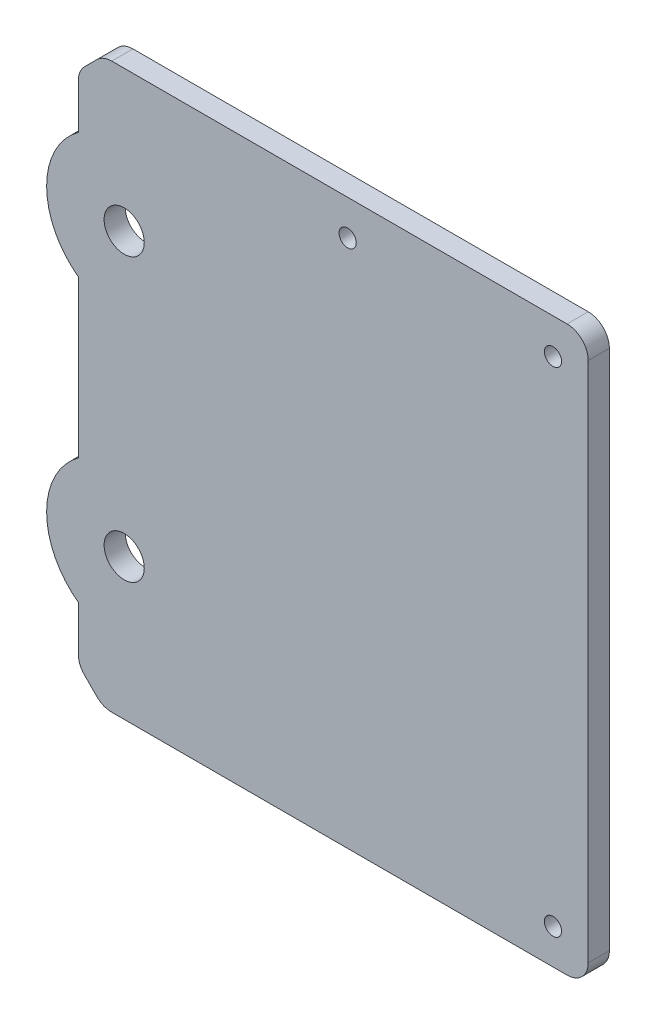
SolidWorks part; units mm, degrees
ref_plane "Front Plane" through (0, 0, 0) normal (0, 0, 1) x (1, 0, 0)
ref_plane "Top Plane" through (0, 0, 0) normal (0, 1, 0) x (1, 0, 0)
ref_plane "Right Plane" through (0, 0, 0) normal (1, 0, 0) x (0, 0, -1)
sketch "Base" plane through (0, 0, 0) normal (0, 0, 1) x (1, 0, 0)
  line L1 (-29.1058, 40) -> (-29.1058, -40)
  line L4 (-17.7758, -40) -> (43.2242, -40)
  line L8 (-22.6058, 20) -> (-22.6058, -20) construction
  line L9 (12.7242, 15.875) -> (12.7242, -32.625) construction
  line L10 (23.8492, 12.75) -> (1.5992, 12.75)
  line L11 (23.8492, 12.75) -> (23.8492, -29.5)
  line L12 (23.8492, -29.5) -> (1.5992, -29.5)
  line L13 (1.5992, 12.75) -> (1.5992, -29.5)
  line L14 (33.2242, 30) -> (33.2242, -30) construction
  line L15 (33.2242, 1) -> (43.2242, 1) construction
  line L16 (43.2242, 40) -> (43.2242, -40)
  line L18 (-17.7758, -40) -> (-29.1058, -40)
  line L19 (33.2242, -30) -> (33.2242, -40) construction
  line L20 (33.2242, 30) -> (43.2242, 40) construction
  line L21 (-29.1058, 40) -> (43.2242, 40)
  line L22 (7.7242, -32.625) -> (17.7242, -32.625)
  line L24 (33.2242, 30) -> (1.5992, 30) construction
  line L25 (1.5992, 30) -> (1.5992, 40) construction
  line L26 (1.5992, -40) -> (1.5992, -30) construction
  line L27 (1.5992, -30) -> (33.2242, -30) construction
  line L28 (7.7242, 15.875) -> (17.7242, 15.875)
  circle A0 centre (12.7242, -20) radius 17.5 construction
  point P2 (30.2242, -20)
  point P7 (24.1741, 0)
  point P9 (12.7242, -40)
  point P10 (-29.1058, 0)
  point P11 (-22.6058, -20)
  point P12 (-22.6058, 20)
  point P15 (-22.6058, 0)
  point P20 (12.7242, 12.75)
  point P22 (23.8492, -8.375)
  point P23 (12.7242, 20)
  point P24 (-22.6058, -20)
  point P25 (-22.6058, 20)
  point P26 (12.7242, 15.875)
  point P27 (12.7242, -32.625)
  point P30 (12.7242, -8.375)
  point P31 (12.7242, -20)
  point P33 (12.7242, -2.5)
  point P41 (38.2242, -35)
  point P43 (38.2242, 35)
  point P44 (9.0992, 35)
  point P45 (1.5992, 35)
  point P46 (38.2242, 1)
  point P47 (33.2242, -35)
  point P48 (7.7242, -32.625)
  point P49 (17.7242, -32.625)
  point P50 (7.7242, 15.875)
  point P51 (17.7242, 15.875)
  dimension "D11" = 35
  dimension "D2" = 42.25
  dimension "D1" = 22.25
  dimension "D4" = 35.33
  dimension "D9" = 48.5
  dimension "D3" = 40
  dimension "D10" = 9.5
  dimension "D5" = 6.5
  dimension "D14" = 10
  dimension "D7" = 80
  dimension "D8" = 10
  dimension "D12" = 3.5
  dimension "D6" = 3
  dimension "D13" = 7.5
  dimension "D15" = 10
sketch "Hole_sketch" plane through (0, 0, 0) normal (0, 0, 1) x (1, 0, 0)
  point P0 (-22.6058, -20)
  point P2 (-22.6058, 20)
  point P4 (12.7242, 15.875)
  point P6 (12.7242, -32.625)
extrude "Main" add sketch "Base" along normal blind 3
hole_wizard "Gear Axis Holes" positions "Sketch9" profile "Sketch8" hole size "Ø5.7" standard "ANSI Metric" end condition through all
sketch "Sketch9" plane through (0, 0, 3) normal (0, 0, -1) x (-1, 0, 0)
  point P0 (22.6058, -20)
  point P3 (22.6058, 20)
sketch "Sketch8" plane through (-22.6058, -20, 3) normal (1, 0, 0) x (0, -1, 0)
  line L0 (0, 0) -> (0, 3)
  line L1 (0, 3) -> (2.85, 3)
  line L2 (2.85, 3) -> (2.85, 0)
  line L5 (2.85, 0) -> (0, 0)
  line L11 (0, -6.35) -> (0, 107.95) construction
  dimension "Thru Hole Dia." = 5.7
  dimension "Thru Hole Depth" = 3
hole_wizard "M1.6 Clearance Hole1" [suppressed] positions "Sketch11" profile "Sketch10" hole size "M1.6" standard "ANSI Metric"
sketch "Sketch11" plane through (0, 0, 3) normal (0, 0, 1) x (1, 0, 0)
  point P7 (17.7242, -32.625)
  point P9 (7.7242, -32.625)
  point P11 (7.7242, 15.875)
  point P13 (17.7242, 15.875)
sketch "Sketch10" plane through (17.7242, -32.625, 3) normal (1, 0, 0) x (0, -1, 0)
  line L0 (0, 0) -> (0, 3)
  line L1 (0, 3) -> (0.7, 3)
  line L2 (0.7, 3) -> (0.7, 0)
  line L5 (0.7, 0) -> (0, 0)
  line L11 (0, -6.35) -> (0, 107.95) construction
  dimension "Thru Hole Dia." = 1.4
  dimension "Thru Hole Depth" = 3
sketch "Sketch13" plane through (0, 0, 3) normal (0, 0, 1) x (1, 0, 0)
  line L10 (33.2242, 30) -> (33.2242, -30) construction
  line L11 (33.2242, 30) -> (1.5992, 30) construction
  line L12 (1.5992, 30) -> (1.5992, 40) construction
  line L13 (-29.1058, 40) -> (43.2242, 40) construction
  line L15 (43.2242, 40) -> (43.2242, -40) construction
  line L17 (33.2242, 30) -> (33.2242, 1)
  line L18 (33.2242, 30) -> (1.5992, 30)
  line L19 (1.5992, 30) -> (1.5992, 40)
  line L20 (1.5992, 40) -> (43.2242, 40)
  line L21 (43.2242, 40) -> (43.2242, 1)
  line L22 (33.2242, -30) -> (33.2242, -40) construction
  line L23 (-17.7758, -40) -> (43.2242, -40) construction
  line L24 (33.2242, -30) -> (33.2242, -40)
  line L25 (33.2242, 30) -> (33.2242, -30)
  line L26 (33.2242, -40) -> (43.2242, -40)
  line L27 (43.2242, 40) -> (43.2242, -40)
  line M42 (-29.1058, -40) -> (43.2242, -40)
  line M44 (43.2242, 40) -> (-29.1058, 40)
  line M60 (43.2242, -40) -> (43.2242, 40)
extrude "Boss-Extrude1" [suppressed] add sketch "Sketch13" along normal blind 18.75 contours L17 L25 L24 L19 L18 M42 M60 M44
fillet "Fillet4" [suppressed] radius 5
fillet "Fillet8" [suppressed] radius 1.5
sketch "Sketch21" [suppressed] plane through (0, 0, 3) normal (0, 0, 1) x (1, 0, 0)
  line L0 (-29.1058, 40) -> (-29.1058, -40) construction
  line L1 (-29.1058, 28.8741) -> (-29.1058, 11.1259)
  line L2 (-29.1058, -11.1259) -> (-29.1058, -28.8741)
  arc A0 (-29.1058, -11.1259) -> (-29.1058, -28.8741) centre (-22.6058, -20) ccw
  arc A1 (-29.1058, 28.8741) -> (-29.1058, 11.1259) centre (-22.6058, 20) ccw
  dimension "D1" = 22
extrude "Boss-Extrude2" [suppressed] add sketch "Sketch21" against normal up to surface (3 mm away)
chamfer "Chamfer1" distance 3.5 angle 45 2 edges at (-29.1058, -40, 1.5) (-29.1058, 40, 1.5)
fillet "Fillet6" radius 3 6 edges at (-25.6058, -40, 1.5) (-29.1058, -36.5, 1.5) (-29.1058, 36.5, 1.5) (-25.6058, 40, 1.5) (43.2242, 40, 1.5) (43.2242, -40, 1.5)
sketch "Sketch14" [suppressed] plane through (0, 0, 3) normal (0, 0, 1) x (1, 0, 0)
  line L0 (8.4742, -32.625) -> (6.9742, -32.625) construction
  line L1 (8.4742, -33.325) -> (6.9742, -33.325)
  line L2 (8.4742, -31.925) -> (6.9742, -31.925)
  line L3 (18.4742, -32.625) -> (16.9742, -32.625) construction
  line L4 (7.7242, -32.625) -> (17.7242, -32.625) construction
  line L5 (18.4742, -33.325) -> (16.9742, -33.325)
  line L6 (18.4742, -31.925) -> (16.9742, -31.925)
  line L7 (-1.3922, -8.375) -> (26.8405, -8.375) construction
  line L8 (8.4742, 15.875) -> (6.9742, 15.875) construction
  line L9 (8.4742, 16.575) -> (6.9742, 16.575)
  line L10 (8.4742, 15.175) -> (6.9742, 15.175)
  line L11 (18.4742, 15.875) -> (16.9742, 15.875) construction
  line L12 (18.4742, 16.575) -> (16.9742, 16.575)
  line L13 (18.4742, 15.175) -> (16.9742, 15.175)
  arc A0 (8.4742, -33.325) -> (8.4742, -31.925) centre (8.4742, -32.625) ccw
  arc A1 (6.9742, -31.925) -> (6.9742, -33.325) centre (6.9742, -32.625) ccw
  arc A2 (18.4742, -33.325) -> (18.4742, -31.925) centre (18.4742, -32.625) ccw
  arc A3 (16.9742, -31.925) -> (16.9742, -33.325) centre (16.9742, -32.625) ccw
  circle A6 centre (17.7242, -32.625) radius 0.7 construction
  arc A7 (8.4742, 16.575) -> (8.4742, 15.175) centre (8.4742, 15.875) cw
  arc A8 (6.9742, 15.175) -> (6.9742, 16.575) centre (6.9742, 15.875) cw
  arc A9 (18.4742, 16.575) -> (18.4742, 15.175) centre (18.4742, 15.875) cw
  arc A10 (16.9742, 15.175) -> (16.9742, 16.575) centre (16.9742, 15.875) cw
  point P2 (7.7242, -32.625)
  point P8 (17.7242, -32.625)
  point P26 (7.7242, 15.875)
  point P33 (17.7242, 15.875)
  dimension "D1" = 1.5
extrude "Cut-Extrude1" [suppressed] cut sketch "Sketch14" against normal through all
hole_wizard "#2 Clearance Hole1" [suppressed] positions "Sketch16" profile "Sketch15" hole size "#2" standard "ANSI Inch"
sketch "Sketch16" [suppressed] plane through (0, 0, 21.75) normal (0, 0, 1) x (1, 0, 0)
  point P1 (9.0992, 35)
  point P3 (38.2242, 35)
  point P5 (38.2242, -35)
sketch "Sketch15" plane through (9.0992, 35, 21.75) normal (1, 0, 0) x (0, -1, 0)
  line L0 (0, 0) -> (0, 21.75)
  line L1 (0, 21.75) -> (1.2192, 21.75)
  line L2 (1.2192, 21.75) -> (1.2192, 0)
  line L5 (1.2192, 0) -> (0, 0)
  line L11 (0, -6.35) -> (0, 107.95) construction
  dimension "Thru Hole Dia." = 2.4384
  dimension "Thru Hole Depth" = 21.75
sketch "Sketch17" [suppressed] plane through (33.2242, 0, 0) normal (-1, 0, 0) x (0, 0, 1)
  line L1 (3, -38.5) -> (21.75, -38.5) construction
  line L2 (14.25, -38.5) -> (14.25, 25) construction
  line L3 (21.75, 25) -> (3, 25) construction
  line L4 (21.75, 25) -> (21.75, -38.5) construction
  line L5 (9.25, 20) -> (9.25, -33.5) construction
  line L6 (3, 35.2574) -> (3, -35.2574) construction
  line L7 (3, 35.2574) -> (3, -35.2574) construction
  line L8 (9.25, 20) -> (9.25, 25) construction
  line L9 (9.25, -33.5) -> (9.25, -38.5) construction
  point P0 (9.25, 20)
  point P1 (9.25, -33.5)
  point P2 (12.375, -38.5)
  point P13 (9.25, -6.75)
  point P16 (3, 0)
  dimension "D1" = 5
  dimension "D2" = 7.5
  dimension "D3" = 5
hole_wizard "M5 Clearance Hole1" [suppressed] positions "Sketch19" profile "Sketch18" hole size "M5" standard "ANSI Metric"
sketch "Sketch19" [suppressed] plane through (33.2242, 0, 0) normal (-1, 0, 0) x (0, 0, 1)
  point P1 (9.25, 20)
  point P3 (9.25, -33.5)
sketch "Sketch18" plane through (33.2242, 20, 9.25) normal (0, 1, 0) x (0, 0, 1)
  line L0 (0, 0) -> (0, 10)
  line L1 (0, 10) -> (2.75, 10)
  line L2 (2.75, 10) -> (2.75, 0)
  line L5 (2.75, 0) -> (0, 0)
  line L11 (0, -6.35) -> (0, 107.95) construction
  dimension "Thru Hole Dia." = 5.5
  dimension "Thru Hole Depth" = 10
sketch "Sketch20" [suppressed] plane through (0, 0, 21.75) normal (0, 0, 1) x (1, 0, 0)
  line L0 (15.0992, 25) -> (15.0992, 40)
  line L2 (40.2242, 40) -> (6.5992, 40) construction
  line L3 (15.0992, 40) -> (33.2242, 40)
  line L4 (33.2242, 40) -> (33.2242, 25)
  line L5 (33.2242, 25) -> (15.0992, 25)
  line L7 (33.2242, 25) -> (33.2242, -38.5) construction
  dimension "D1" = 13.5
extrude "Cut-Extrude2" [suppressed] cut sketch "Sketch20" against normal up to surface (18.75 mm away)
fillet "Fillet7" [suppressed] radius 5
hole_wizard "#2 Clearance Hole2" positions "Sketch22" profile "Sketch23" hole size "#2" standard "ANSI Inch" end condition through all
sketch "Sketch22" plane through (0, 0, 3) normal (0, 0, 1) x (1, 0, 0)
  point P1 (9.0992, 35)
  point P3 (38.2242, 35)
  point P5 (38.2242, -35)
sketch "Sketch23" plane through (9.0992, 35, 3) normal (1, 0, 0) x (0, -1, 0)
  line L0 (0, 0) -> (0, 3)
  line L1 (0, 3) -> (1.2192, 3)
  line L2 (1.2192, 3) -> (1.2192, 0)
  line L5 (1.2192, 0) -> (0, 0)
  line L11 (0, -6.35) -> (0, 107.95) construction
  dimension "Thru Hole Dia." = 2.4384
  dimension "Thru Hole Depth" = 3
sketch "Sketch24" plane through (0, 0, 3) normal (0, 0, 1) x (1, 0, 0)
  line L0 (-29.1058, 40) -> (-29.1058, -40) construction
  line L1 (-29.1058, 28.8741) -> (-29.1058, 11.1259)
  line L2 (-29.1058, -11.1259) -> (-29.1058, -28.8741)
  arc A0 (-29.1058, -11.1259) -> (-29.1058, -28.8741) centre (-22.6058, -20) ccw
  arc A1 (-29.1058, 28.8741) -> (-29.1058, 11.1259) centre (-22.6058, 20) ccw
  point P0 (-22.6058, 20)
  point P2 (-22.6058, -20)
  dimension "D1" = 22
extrude "Boss-Extrude4" add sketch "Sketch24" against normal up to surface (3 mm away) up to face at (10.3184, 35, 0)
equation "\"D_gear-axes\"= 40mm"
equation "\"D_gear-servo\"= 35mm"
equation "\"W_servo\"= 41.5mm"
equation "\"W_servo-center\"= 9.50mm"
equation "\"D1@Base\"=\"L_servo\"+0.75"
equation "\"D2@Base\"=\"W_servo\"+0.75"
equation "\"L_servo\"= 21.5mm"
equation "\"D4@Base\"=\"D_gear-servo\" + 0.33"
equation "\"D9@Base\"=\"D_servo-holes\""
equation "\"D_servo-holes\"= 48.5mm"
equation "\"D3@Base\"=\"D_gear-axes\""
equation "\"D10@Base\"=\"W_servo-center\""
